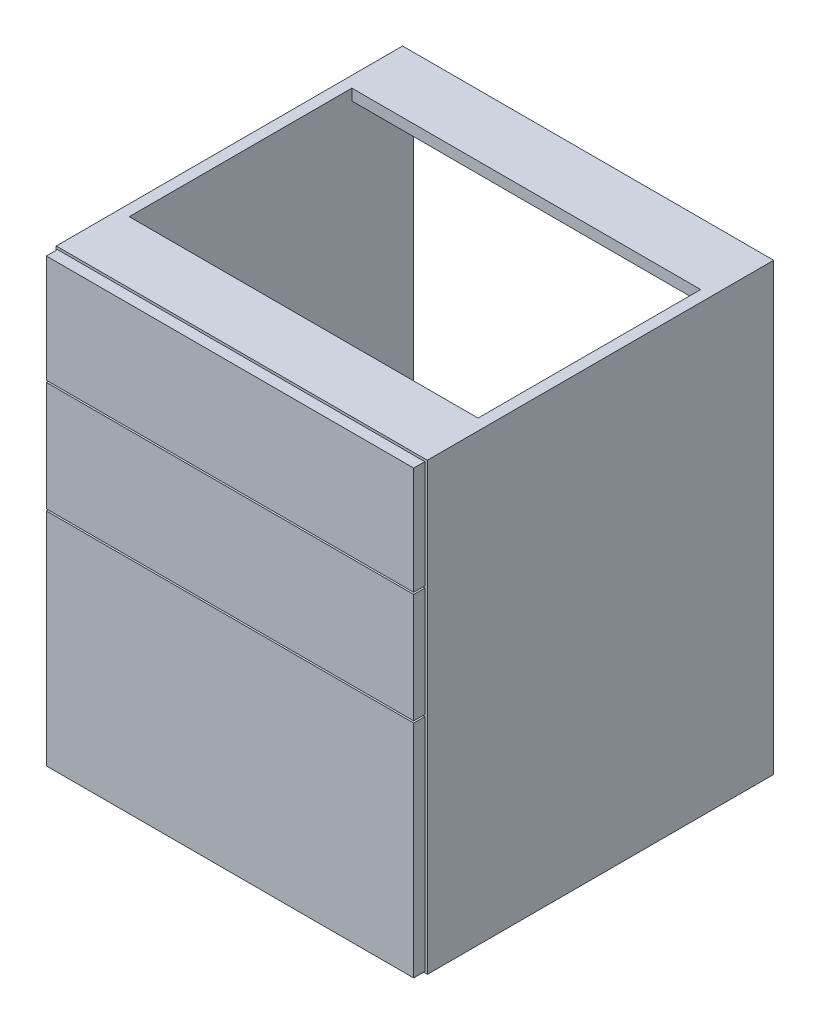
SolidWorks part; units mm, degrees
ref_plane "Front Plane" through (0, 0, 0) normal (0, 0, 1) x (1, 0, 0)
ref_plane "Top Plane" through (0, 0, 0) normal (0, 1, 0) x (1, 0, 0)
ref_plane "Right Plane" through (0, 0, 0) normal (1, 0, 0) x (0, 0, -1)
sketch "Sketch1" plane through (0, 0, 0) normal (0, 0, 1) x (1, 0, 0)
  line L1 (0, 0) -> (600, 0)
  line L2 (0, 0) -> (0, 720)
  line L3 (0, 720) -> (600, 720)
  line L4 (600, 0) -> (600, 720)
  dimension "D1" = 600
  dimension "D2" = 720
extrude "Boss-Extrude1" add sketch "Sketch1" against normal blind 560
sketch "Sketch2" plane through (0, 0, 0) normal (0, 0, 1) x (1, 0, 0)
  line L0 (600, 720) -> (0, 720) construction
  line L1 (18, 702) -> (582, 702)
  line L2 (18, 702) -> (18, 18)
  line L3 (18, 18) -> (582, 18)
  line L4 (582, 702) -> (582, 18)
  line L5 (600, 0) -> (600, 720) construction
  line L6 (0, 720) -> (0, 0) construction
  line L7 (0, 0) -> (600, 0) construction
  dimension "D1" = 18
  dimension "D2" = 18
  dimension "D3" = 18
  dimension "D4" = 18
extrude "Cut-Extrude1" cut sketch "Sketch2" against normal through all
sketch "Sketch3" plane through (0, 720, 0) normal (0, 1, 0) x (1, 0, 0)
  line L0 (0, 560) -> (0, 0) construction
  line L1 (18, 460) -> (582, 460)
  line L2 (18, 460) -> (18, 100)
  line L3 (18, 100) -> (582, 100)
  line L4 (582, 460) -> (582, 100)
  line L5 (600, 560) -> (600, 0) construction
  line L6 (600, 560) -> (0, 560) construction
  line L7 (600, 0) -> (0, 0) construction
  dimension "D1" = 18
  dimension "D2" = 18
  dimension "D3" = 100
  dimension "D4" = 100
extrude "Cut-Extrude2" cut sketch "Sketch3" against normal up to surface (702 mm away) up to face at (300, 18, -280)
ref_plane "Plane1" through (0, 0, 1) normal (0, 0, 1) x (1, 0, 0)
sketch "Sketch4" plane through (0, 0, 1) normal (0, 0, 1) x (1, 0, 0)
  line L0 (600, 720) -> (0, 720) construction
  line L1 (3, 717) -> (597, 717)
  line L2 (3, 717) -> (3, 3)
  line L3 (3, 3) -> (597, 3)
  line L4 (597, 717) -> (597, 3)
  line L5 (600, 0) -> (600, 720) construction
  line L6 (0, 720) -> (0, 0) construction
  line L7 (0, 0) -> (600, 0) construction
  dimension "D1" = 3
  dimension "D2" = 3
  dimension "D3" = 3
  dimension "D4" = 3
extrude "Boss-Extrude2" add sketch "Sketch4" along normal blind 18 separate body
sketch "Sketch5" plane through (0, 0, 19) normal (0, 0, 1) x (1, 0, 0)
  line L0 (597, 3) -> (597, 717) construction
  line L1 (597, 360) -> (3, 360)
  line L2 (597, 360) -> (597, 363)
  line L3 (597, 363) -> (3, 363)
  line L4 (3, 360) -> (3, 363)
  line L5 (3, 717) -> (3, 3) construction
  line L6 (600, 0) -> (600, 720) construction
  line L7 (0, 720) -> (0, 0) construction
  dimension "D1" = 3
  dimension "D2" = 3
  dimension "D3" = 3
extrude "Cut-Extrude3" cut sketch "Sketch5" against normal blind 18
sketch "Sketch6" plane through (0, 0, 19) normal (0, 0, 1) x (1, 0, 0)
  line L0 (3, 717) -> (3, 363) construction
  line L1 (3, 540) -> (597, 540)
  line L2 (3, 540) -> (3, 543)
  line L3 (3, 543) -> (597, 543)
  line L4 (597, 540) -> (597, 543)
  line L5 (597, 363) -> (597, 717) construction
  line L6 (600, 0) -> (600, 720) construction
  line L7 (0, 720) -> (0, 0) construction
  dimension "D1" = 3
  dimension "D2" = 3
  dimension "D3" = 3
extrude "Cut-Extrude4" cut sketch "Sketch6" against normal blind 18
